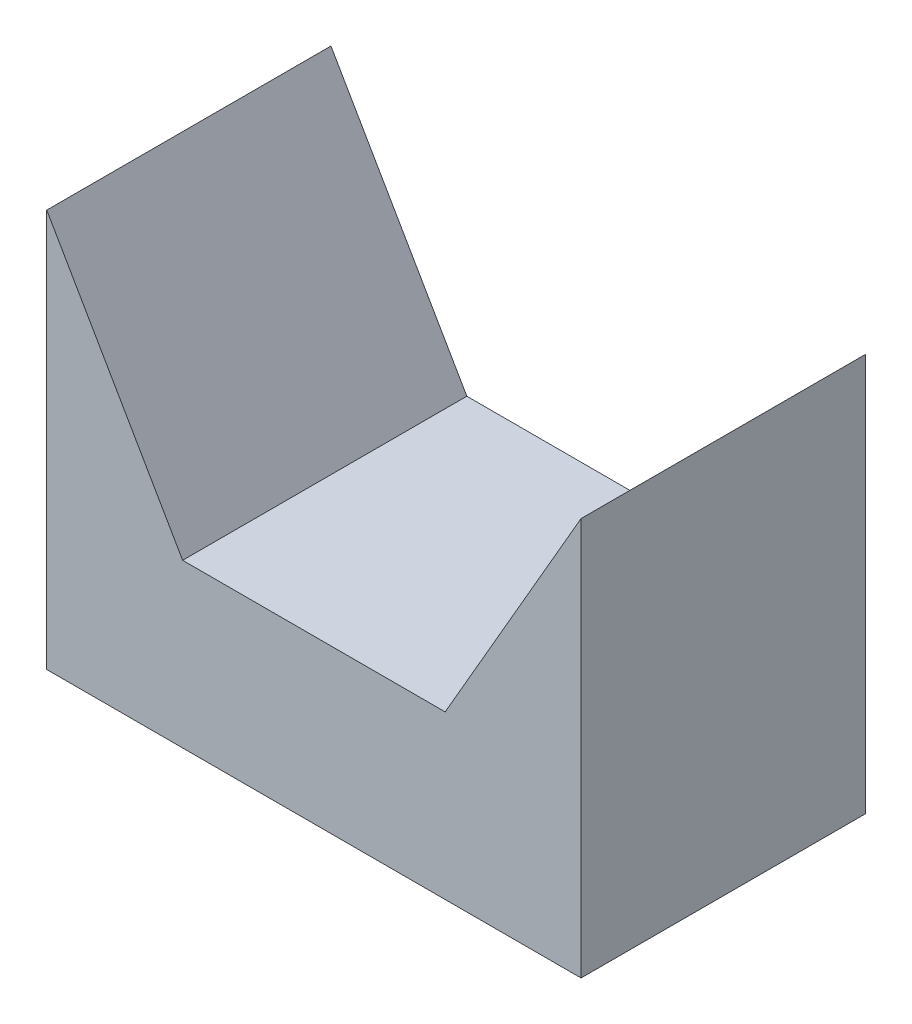
SolidWorks part; units mm, degrees
ref_plane "Ön Düzlem" through (0, 0, 0) normal (0, 0, 1) x (1, 0, 0)
ref_plane "Üst Düzlem" through (0, 0, 0) normal (0, 1, 0) x (1, 0, 0)
ref_plane "Sağ Düzlem" through (0, 0, 0) normal (1, 0, 0) x (0, 0, -1)
sketch "Çizim1" plane through (0, 0, 4.1156) normal (0, 0, 1) x (1, 0, 0)
  line L20 (-4.7, 0.1406) -> (-4.7, -6.8594)
  line L27 (-4.7, -6.8594) -> (4.7, -6.8594)
  line L28 (4.7, -6.8594) -> (4.7, 0.1406)
  line L31 (-4.7, 0.1406) -> (-2.3094, -4)
  line L32 (-2.3094, -4) -> (2.3094, -4)
  line L33 (2.3094, -4) -> (4.7, 0.1406)
  line L37 (2.3094, 4) -> (-2.3094, 4) [skipped]
  line L38 (-2.3094, 4) -> (-4.6188, 0) [skipped]
  line L39 (4.6188, 0) -> (2.3094, 4) [skipped]
  circle A0 centre (0, 0) radius 4 construction
  dimension "D2" = 9.4
  dimension "D1" = 7
extrude "Yükseklik-Ekstrüzyon1" add sketch "Çizim1" along normal blind 5
